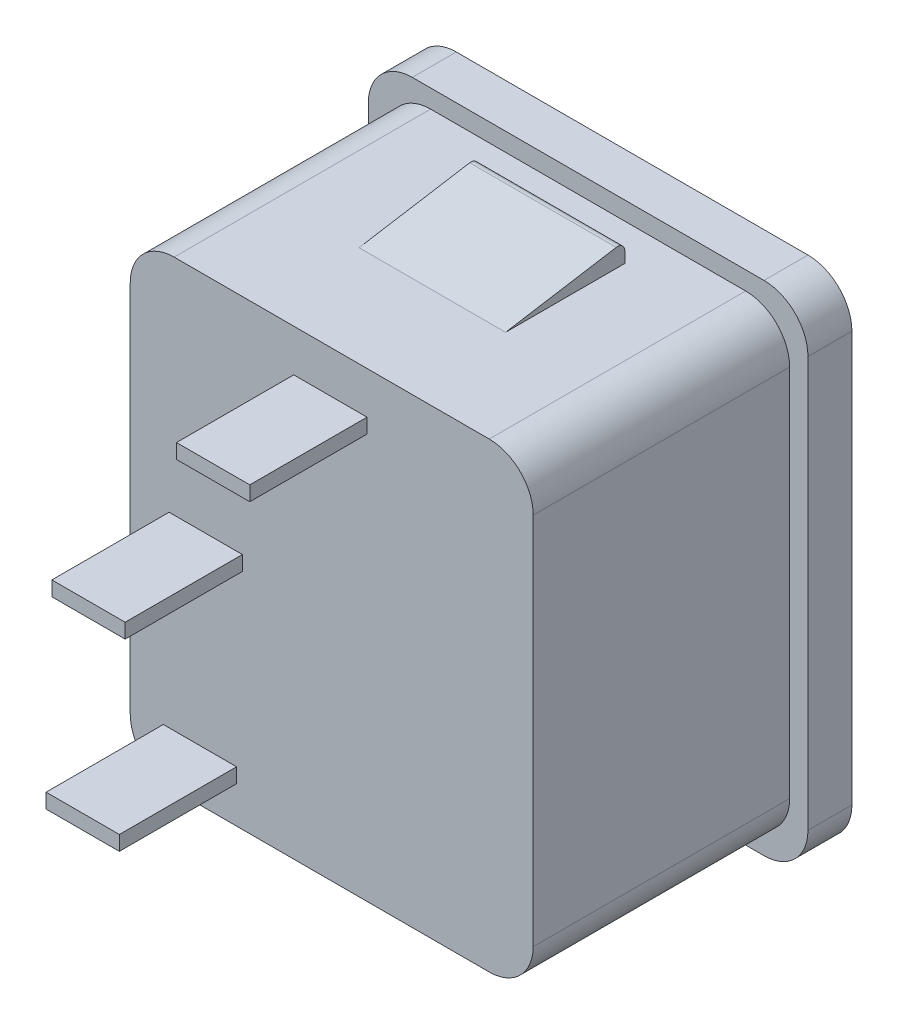
SolidWorks part; units mm, degrees
ref_plane "Front Plane" through (0, 0, 0) normal (0, 0, 1) x (1, 0, 0)
ref_plane "Top Plane" through (0, 0, 0) normal (0, 1, 0) x (1, 0, 0)
ref_plane "Right Plane" through (0, 0, 0) normal (1, 0, 0) x (0, 0, -1)
sketch "Sketch1" plane through (0, 0, 0) normal (0, 0, 1) x (1, 0, 0)
  line L1 (-15, -17) -> (15, -17)
  line L2 (-15, -17) -> (-15, 17)
  line L3 (-15, 17) -> (15, 17)
  line L4 (15, -17) -> (15, 17)
  line L5 (-15, -17) -> (15, 17) construction
  line L6 (-15, 17) -> (15, -17) construction
  point P0 (0, 0)
  dimension "D1" = 30
  dimension "D2" = 34
extrude "Boss-Extrude1" add sketch "Sketch1" against normal blind 3
sketch "Sketch3" plane through (0, 0, 0) normal (0, 0, 1) x (1, 0, 0)
  line L1 (-13.75, -15.75) -> (13.75, -15.75)
  line L2 (-13.75, -15.75) -> (-13.75, 15.75)
  line L3 (-13.75, 15.75) -> (13.75, 15.75)
  line L4 (13.75, -15.75) -> (13.75, 15.75)
  line L5 (-13.75, -15.75) -> (13.75, 15.75) construction
  line L6 (-13.75, 15.75) -> (13.75, -15.75) construction
  point P0 (0, 0)
  dimension "D1" = 31.5
  dimension "D2" = 27.5
extrude "Boss-Extrude2" add sketch "Sketch3" along normal blind 25.5
fillet "Fillet1" radius 3 8 edges at (13.75, 15.75, 12.75) (-13.75, 15.75, 12.75) (-13.75, -15.75, 12.75) (13.75, -15.75, 12.75) (15, -17, -1.5) (-15, -17, -1.5) (15, 17, -1.5) (-15, 17, -1.5)
sketch "Sketch4" plane through (0, 0, 0) normal (1, 0, 0) x (0, 0, -1)
  line L0 (-2.5, 15.75) -> (-2.5, 16.5)
  line L1 (-3.0812, 16.9934) -> (-10.6362, 15.75)
  line L3 (0, 15.75) -> (-25.5, 15.75) construction
  line L4 (0, 17) -> (0, 14) construction
  line L5 (-2.5, 15.75) -> (-10.6362, 15.75)
  line L6 (0, 17) -> (3, 17) construction
  line L7 (0, 0) -> (-16.8329, 0) construction
  line L8 (-2.5, -15.75) -> (-10.6362, -15.75)
  line L9 (-3.0812, -16.9934) -> (-10.6362, -15.75)
  line L10 (-2.5, -15.75) -> (-2.5, -16.5)
  arc A0 (-2.5, 16.5) -> (-3.0812, 16.9934) centre (-3, 16.5) ccw
  arc A1 (-2.5, -16.5) -> (-3.0812, -16.9934) centre (-3, -16.5) cw
  dimension "D2" = 0.5
  dimension "D1" = 2.5
extrude "Boss-Extrude3" add sketch "Sketch4" along normal mid plane 10
sketch "Sketch5" plane through (0, 0, 25.5) normal (0, 0, 1) x (1, 0, 0)
  line L1 (-11.0976, 0.5) -> (-6.0976, 0.5)
  line L2 (-11.0976, 0.5) -> (-11.0976, -0.5)
  line L3 (-11.0976, -0.5) -> (-6.0976, -0.5)
  line L4 (-6.0976, 0.5) -> (-6.0976, -0.5)
  line L5 (-11.0976, 0.5) -> (-6.0976, -0.5) construction
  line L6 (-11.0976, -0.5) -> (-6.0976, 0.5) construction
  line L7 (-2.5921, 12.8716) -> (2.4079, 12.8716)
  line L8 (-2.5921, 12.8716) -> (-2.5921, 11.8716)
  line L9 (-2.5921, 11.8716) -> (2.4079, 11.8716)
  line L10 (2.4079, 12.8716) -> (2.4079, 11.8716)
  line L11 (-2.5921, 12.8716) -> (2.4079, 11.8716) construction
  line L12 (-2.5921, 11.8716) -> (2.4079, 12.8716) construction
  line L13 (-11.4932, -12.2419) -> (-6.4932, -12.2419)
  line L14 (-11.4932, -12.2419) -> (-11.4932, -13.2419)
  line L15 (-11.4932, -13.2419) -> (-6.4932, -13.2419)
  line L16 (-6.4932, -12.2419) -> (-6.4932, -13.2419)
  line L17 (-11.4932, -12.2419) -> (-6.4932, -13.2419) construction
  line L18 (-11.4932, -13.2419) -> (-6.4932, -12.2419) construction
  point P0 (-8.5976, 0)
  point P5 (-0.0921, 12.3716)
  point P10 (2.4024, 10.2062)
  point P11 (-8.9932, -12.7419)
  point P16 (1.8209, 13.6949)
  point P17 (0, 13.5902)
  point P18 (-8.3185, 5.9372)
  point P19 (-8.9932, -12.7419)
  point P20 (-8.5976, 0)
  point P21 (-0.0921, 12.3716)
  dimension "D1" = 5
  dimension "D2" = 1
extrude "Cut-Extrude1" cut sketch "Sketch5" against normal blind 8 flip side to cut
